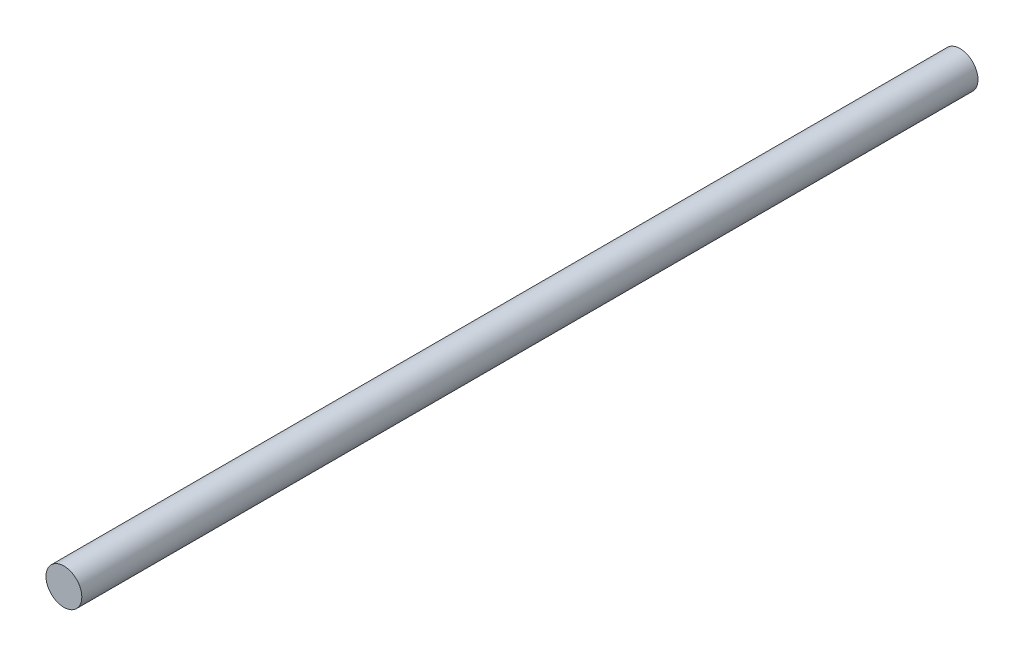
SolidWorks part; units mm, degrees
ref_plane "Plano frontal" through (0, 0, 0) normal (0, 0, 1) x (1, 0, 0)
ref_plane "Plano superior" through (0, 0, 0) normal (0, 1, 0) x (1, 0, 0)
ref_plane "Plano direito" through (0, 0, 0) normal (1, 0, 0) x (0, 0, -1)
sketch "Esboço1" plane through (0, 0, 0) normal (0, 0, 1) x (1, 0, 0)
  circle A0 centre (0, 0) radius 10
  dimension "D1" = 20
extrude "Ressalto-extrusão1" add sketch "Esboço1" along normal blind 500
